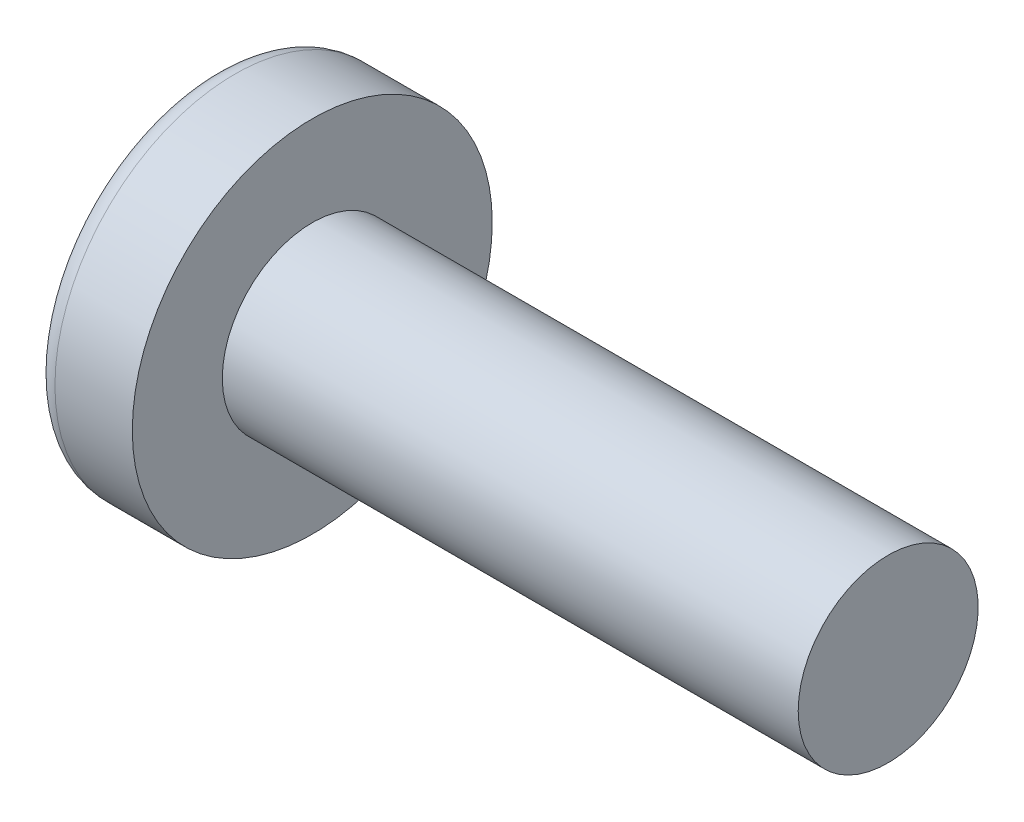
SolidWorks part; units mm, degrees
ref_plane "Plane1" through (0, 0, 0) normal (0, 0, 1) x (1, 0, 0)
ref_plane "Plane2" through (0, 0, 0) normal (0, 1, 0) x (1, 0, 0)
ref_plane "Plane3" through (0, 0, 0) normal (1, 0, 0) x (0, 0, -1)
sketch "BodySke" plane through (0, 0, 0) normal (0, 0, 1) x (1, 0, 0)
  line L0 (2.1, 1.25) -> (2.1, 2.5)
  line L1 (2.55, 6.35) -> (2.55, -3.175) construction
  line L2 (-25.4, 0) -> (127, 0) construction
  line L3 (10.1, 0) -> (0, 0)
  line L4 (2.1, 1.25) -> (10.1, 1.25)
  line L5 (10.1, 1.25) -> (10.1, 0)
  line L6 (1.0251, 2.5) -> (2.1, 2.5)
  line L7 (2.1, -1.25) -> (10.1, -1.25) construction
  line L8 (2.1, 6.35) -> (2.1, -3.175) construction
  arc A0 (0.7839, 2.3784) -> (0, 0) centre (4, 0) ccw
  arc A2 (0.7839, 2.3784) -> (1.0251, 2.5) centre (1.0251, 2.2) cw
  dimension "Head_fillet_rad" = 0.3
  dimension "Head_crown_rad" = 4
  dimension "Head_ht" = 2.1
  dimension "Diameter" = 2.5
  dimension "Length" = 8
  dimension "Head_dia" = 5
  dimension "Advance" = 0.45
  dimension "Thread_nom" = 8
revolve "Base-Revolve" add sketch "BodySke" angle 360 about L2
cosmetic thread "ThreadCosmetic" [suppressed] parameters "Thread_length"=7.55, "Thread_minor"=1.993
sketch "Sketch3" plane through (0, 0, 0) normal (1, 0, 0) x (0, 0, -1)
  line L0 (0.35, -1.34) -> (-0.35, -1.34)
  line L1 (0.35, -1.34) -> (0.35, 1.34)
  line L2 (-0.35, 1.34) -> (0.35, 1.34)
  line L3 (-0.35, 1.34) -> (-0.35, -1.34)
  dimension "D1" = 1.34
  dimension "Cross_dia" = 2.68
  dimension "D2" = 0.35
  dimension "Cross_width" = 0.7
ref_plane "Plane4" through (1.53, 0, 0) normal (1, 0, 0) x (0, 0, -1)
sketch "Sketch4" plane through (1.53, 0, 0) normal (1, 0, 0) x (0, 0, -1)
  line L0 (0.175, -0.175) -> (-0.175, -0.175)
  line L1 (0.175, -0.175) -> (0.175, 0.175)
  line L2 (-0.175, 0.175) -> (0.175, 0.175)
  line L3 (-0.175, 0.175) -> (-0.175, -0.175)
  dimension "D1" = 0.35
  dimension "D2" = 0.35
  dimension "D3" = 0.175
  dimension "D4" = 0.175
loft "Cut-Loft1" cut profiles "Sketch3", "Sketch4"
pattern_circular "CirPattern1" count 2 every 90 about axis through (0, 0, 0) along (1, 0, 0) of "Cut-Loft1"
sketch "ThdSchSke" [suppressed] plane through (0, 0, 0) normal (0, 0, 1) x (1, 0, 0)
  line L0 (9, -4.172) -> (8.4202, -5)
  line L1 (9, -4.172) -> (9.5798, -5)
  line L2 (9.5798, -5) -> (9.5798, -6.25)
  line L3 (-3.175, 0) -> (5.1513, 0) construction
  line L5 (9.5798, -6.25) -> (8.4202, -6.25)
  line L6 (8.4202, -6.25) -> (8.4202, -5)
  dimension "Thread_minor" = 1.993
  dimension "Diameter" = 2.5
  dimension "Start" = 2.55
  dimension "SideAngle" = 55
  dimension "VeeAngle" = 70
  dimension "Overcut" = 3.125
revolve "ThreadSchematic" [suppressed] cut sketch "ThdSchSke" angle 360 about L3
pattern_linear "ThdSchPat" [suppressed]
equation "\"D1@Sketch3\" = \"Cross_dia@Sketch3\" / 2"
equation "\"D2@Sketch3\" = \"Cross_width@Sketch3\" / 2"
equation "\"D1@Sketch4\" = \"Cross_width@Sketch3\" *.5"
equation "\"D2@Sketch4\" = \"D1@Sketch4\""
equation "\"D3@Sketch4\" = \"D1@Sketch4\" / 2"
equation "\"D4@Sketch4\" = \"D2@Sketch4\" / 2"
equation "\"Thread_length@ThreadCosmetic\" = ((sgn( (\"Length@BodySke\" - \"Advance@BodySke\" ) - \"Thread_nom@BodySke\" )-1)*( (\"Length@BodySke\" - \"Advance@BodySke\" ) - \"Thread_nom@BodySke\" ))/-2+ \"Thread_nom@BodySke\""
equation "\"Thread_minor@ThdSchSke\" = \"Thread_minor@ThreadCosmetic\""
equation "\"Diameter@ThdSchSke\" = \"Diameter@BodySke\""
equation "\"Overcut@ThdSchSke\" = \"Diameter@BodySke\" * 1.25"
equation "\"Start@ThdSchSke\" = \"Head_ht@BodySke\" + \"Length@BodySke\" - \"Thread_length@ThreadCosmetic\"  '---Non-countersunk---"
equation "\"Num_threads@ThdSchPat\" = int( \"Thread_length@ThreadCosmetic\" / \"Advance@BodySke\" + 0.999 )  + 1"
equation "\"Advance@ThdSchPat\" = \"Thread_length@ThreadCosmetic\" /  (\"Num_threads@ThdSchPat\" - 1) 'relax it"
